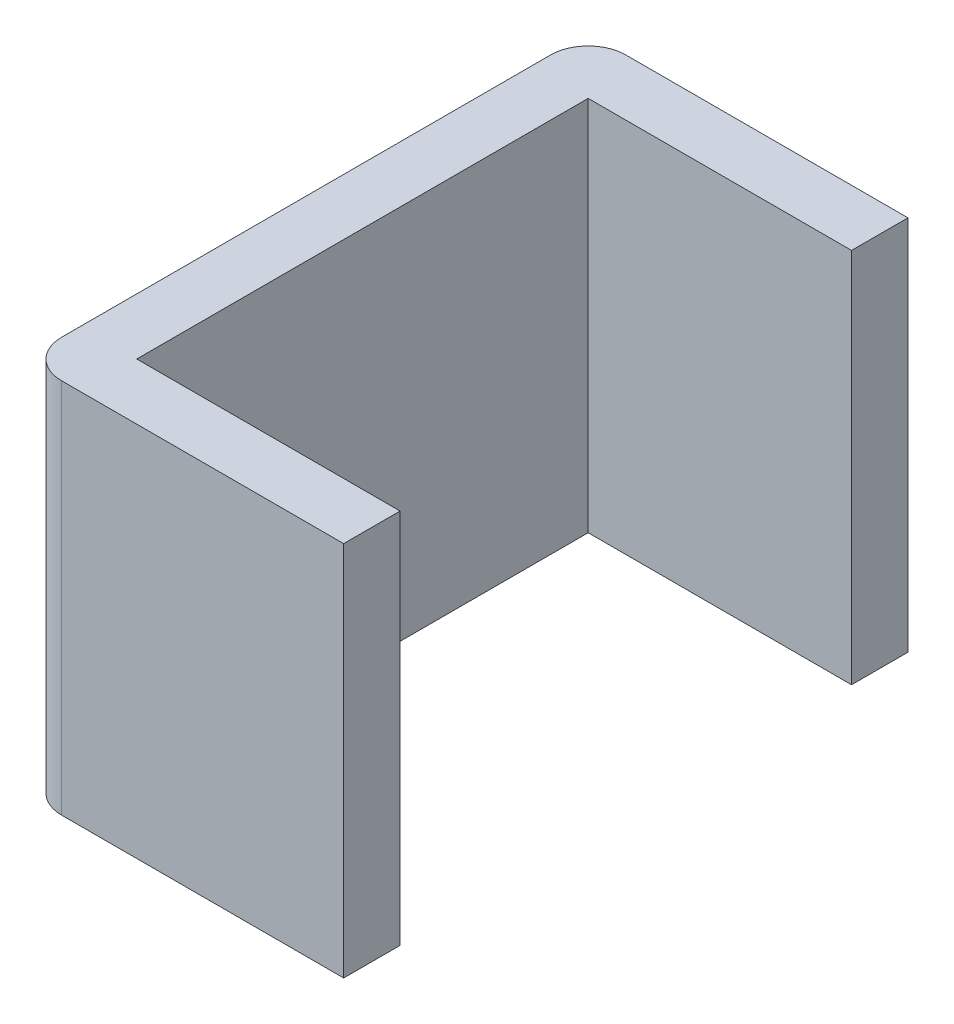
SolidWorks part; units mm, degrees
ref_plane "Front Plane" through (0, 0, 0) normal (0, 0, 1) x (1, 0, 0)
ref_plane "Top Plane" through (0, 0, 0) normal (0, 1, 0) x (1, 0, 0)
ref_plane "Right Plane" through (0, 0, 0) normal (1, 0, 0) x (0, 0, -1)
sketch "Sketch1" plane through (0, 0, 0) normal (0, 1, 0) x (1, 0, 0)
  line L0 (0, 0) -> (-17, 0)
  line L1 (-17, 0) -> (-17, 30)
  line L2 (-17, 30) -> (0, 30)
  line L3 (0, 3) -> (-14, 3)
  line L4 (-14, 3) -> (-14, 27)
  line L5 (-14, 27) -> (0, 27)
  line L6 (0, 30) -> (0, 27)
  line L7 (0, 3) -> (0, 0)
  dimension "D1" = 30
  dimension "1.7" = 17
  dimension "D2" = 3
extrude "Boss-Extrude1" add sketch "Sketch1" along normal blind 20
fillet "Fillet1" radius 2 2 edges at (-17, 10, -30) (-17, 10, 0)
